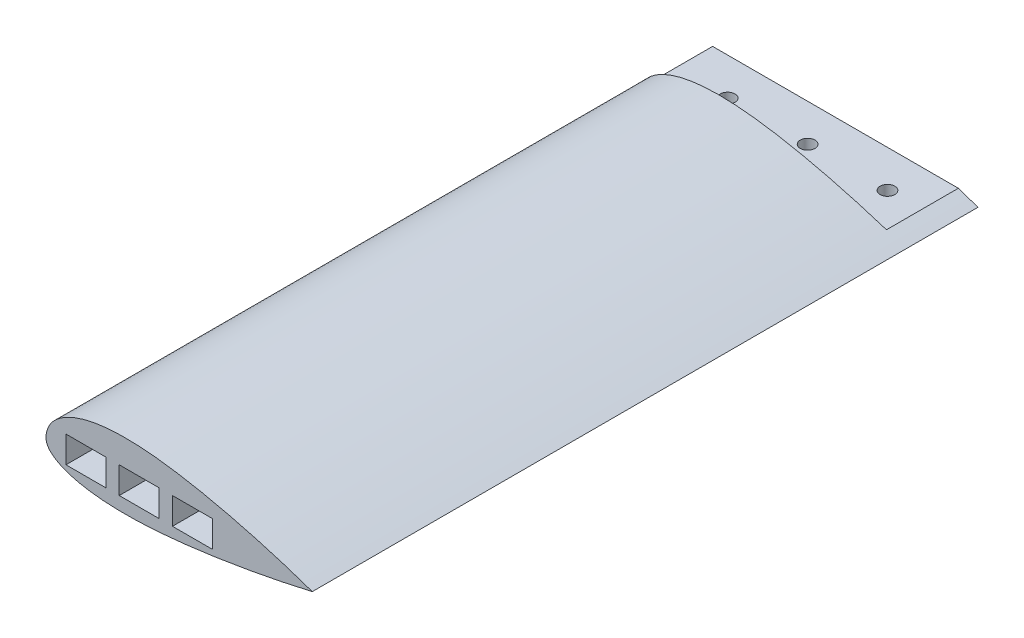
SolidWorks part; units mm, degrees
ref_plane "Front Plane" through (0, 0, 0) normal (0, 0, 1) x (1, 0, 0)
ref_plane "Top Plane" through (0, 0, 0) normal (0, 1, 0) x (1, 0, 0)
ref_plane "Right Plane" through (0, 0, 0) normal (1, 0, 0) x (0, 0, -1)
sketch "Sketch1" plane through (0, 0, 0) normal (0, 0, 1) x (1, 0, 0)
  spline S0 degree 4 poles (0, 0) (0.0009, 0.3297) (0.0295, 0.9275) (0.1439, 1.7967) (0.437, 2.9181) (0.8549, 3.9907) (1.4315, 5.0756) (2.1923, 6.1773) (3.2003, 7.33) (4.4959, 8.5106) (6.154, 9.7149) (8.2741, 10.9292) (10.957, 12.1146) (14.1477, 13.1525) (18.0405, 14.0363) (23.1343, 14.7366) (29.2357, 15.0274) (35.338, 14.8248) (41.1011, 14.3138) (46.841, 13.5968) (51.6037, 12.8505) (56.3456, 11.9834) (61.0671, 11.0139) (64.8328, 10.183) (68.5865, 9.3015) (72.3294, 8.3726) (76.0598, 7.3994) (79.3157, 6.5093) (82.096, 5.721) (84.4127, 5.0444) (86.2537, 4.4957) (88.1107, 3.9294) (89.9289, 3.3646) (91.806, 2.7666) (93.571, 2.1956) (95.5202, 1.5463) (97.1384, 1.0009) (99.1531, 0.3002) (100.3626, -0.127) (101.915, -0.6848) (103.1337, -1.1307) (104.3912, -1.5976) (105.6393, -2.0687) (106.8855, -2.5467) (108.1291, -3.0316) (109.0597, -3.4006) (109.6792, -3.6489) (109.9887, -3.7737) knots 0 0 0 0 0 0.011046 0.020082 0.029326 0.038802 0.04958 0.06121 0.074146 0.090071 0.108265 0.129827 0.155965 0.188307 0.220649 0.263591 0.328276 0.39296 0.425303 0.457645 0.522329 0.554672 0.587014 0.619356 0.651699 0.684041 0.716383 0.748725 0.764896 0.781068 0.797239 0.81341 0.829581 0.845752 0.861923 0.878094 0.894265 0.910437 0.921632 0.932827 0.944023 0.955218 0.966414 0.977609 0.988805 1 1 1 1 1 construction
  spline S1 degree 4 poles (0, 0) (0.0009, 0.3297) (0.0295, 0.9275) (0.1439, 1.7967) (0.437, 2.9181) (0.8549, 3.9907) (1.4315, 5.0756) (2.1923, 6.1773) (3.2003, 7.33) (4.4959, 8.5106) (6.154, 9.7149) (8.2741, 10.9292) (10.957, 12.1146) (14.1477, 13.1525) (18.0405, 14.0363) (23.1343, 14.7366) (29.2357, 15.0274) (35.338, 14.8248) (41.1011, 14.3138) (46.841, 13.5968) (51.6037, 12.8505) (56.3456, 11.9834) (61.0671, 11.0139) (64.8328, 10.183) (68.5865, 9.3015) (72.3294, 8.3726) (76.0598, 7.3994) (79.3157, 6.5093) (82.096, 5.721) (84.4127, 5.0444) (86.2537, 4.4957) (88.1107, 3.9294) (89.9289, 3.3646) (91.806, 2.7666) (93.571, 2.1956) (95.5202, 1.5463) (97.1383, 1.0009) (98.7751, 0.4317) (99.5867, 0.1465) (100.0002, 0) knots 0 0 0 0 0 0.011046 0.020082 0.029326 0.038802 0.04958 0.06121 0.074146 0.090071 0.108265 0.129827 0.155965 0.188307 0.220649 0.263591 0.328276 0.39296 0.425303 0.457645 0.522329 0.554672 0.587014 0.619356 0.651699 0.684041 0.716383 0.748725 0.764896 0.781068 0.797239 0.81341 0.829581 0.845752 0.861923 0.878094 0.894265 0.910434 0.910434 0.910434 0.910434 0.910434
  spline S2 degree 4 poles (0, 0) (0.0003, -0.1693) (0.016, -0.4614) (0.0775, -0.8851) (0.2333, -1.4356) (0.4512, -1.9609) (0.763, -2.5157) (1.1968, -3.1118) (1.8009, -3.7667) (2.6459, -4.4954) (3.845, -5.3152) (5.5202, -6.2106) (7.8905, -7.1807) (10.9471, -8.0963) (15.4296, -9.0396) (21.208, -9.73) (27.9775, -10.0275) (35.6486, -9.8891) (42.3469, -9.4657) (48.0748, -8.9399) (53.7915, -8.3061) (59.4968, -7.5766) (65.1885, -6.7461) (70.8667, -5.8302) (75.5899, -5.0142) (79.3624, -4.3307) (82.6596, -3.7058) (85.4801, -3.1515) (87.5962, -2.7233) (89.0005, -2.4341) (90.1811, -2.1872) (91.104, -1.9926) (92.3051, -1.7354) (93.6554, -1.4439) (95.3898, -1.0596) (97.1027, -0.6748) (99.4365, -0.1347) (101.1191, 0.2637) (103.9947, 0.9599) (105.7889, 1.4169) (107.9207, 1.9617) (109.0082, 2.2534) (109.6995, 2.4359) (109.9984, 2.5166) knots 0 0 0 0 0 0.005887 0.010193 0.014867 0.019889 0.025655 0.032315 0.040498 0.050865 0.064448 0.082823 0.106556 0.139954 0.175459 0.242256 0.309053 0.375849 0.442646 0.476045 0.509443 0.57624 0.643037 0.676435 0.709833 0.743232 0.77663 0.793329 0.810028 0.818378 0.826728 0.835077 0.843427 0.860126 0.876825 0.893524 0.910224 0.932668 0.955112 0.977556 0.988778 1 1 1 1 1 construction
  spline S3 degree 4 poles (0, 0) (0.0003, -0.1693) (0.016, -0.4614) (0.0775, -0.8851) (0.2333, -1.4356) (0.4512, -1.9609) (0.763, -2.5157) (1.1968, -3.1118) (1.8009, -3.7667) (2.6459, -4.4954) (3.845, -5.3152) (5.5202, -6.2106) (7.8905, -7.1807) (10.9471, -8.0963) (15.4296, -9.0396) (21.208, -9.73) (27.9775, -10.0275) (35.6486, -9.8891) (42.3469, -9.4657) (48.0748, -8.9399) (53.7915, -8.3061) (59.4968, -7.5766) (65.1885, -6.7461) (70.8667, -5.8302) (75.5899, -5.0142) (79.3624, -4.3307) (82.6596, -3.7058) (85.4801, -3.1515) (87.5962, -2.7233) (89.0005, -2.4341) (90.1811, -2.1872) (91.104, -1.9926) (92.3051, -1.7354) (93.6554, -1.4439) (95.3898, -1.0596) (97.1027, -0.6748) (98.7145, -0.3018) (99.5756, -0.1002) (100.0002, 0) knots 0 0 0 0 0 0.005887 0.010193 0.014867 0.019889 0.025655 0.032315 0.040498 0.050865 0.064448 0.082823 0.106556 0.139954 0.175459 0.242256 0.309053 0.375849 0.442646 0.476045 0.509443 0.57624 0.643037 0.676435 0.709833 0.743232 0.77663 0.793329 0.810028 0.818378 0.826728 0.835077 0.843427 0.860126 0.876825 0.893524 0.910224 0.910224 0.910224 0.910224 0.910224
sketch "Sketch2" plane through (0, 0, 0) normal (0, 1, 0) x (1, 0, 0)
  line L1 (0, 0) -> (0, -250) construction
  line L2 (0, -250) -> (50, -500) construction
  spline S0 degree 2 poles (0, 0) (0, -250) (50, -500) knots 0 0 0 1 1 1
  dimension "D1" = 250
  dimension "D2" = 250
  dimension "D3" = 50
ref_plane "Plane2" through (0, 0, 500) normal (0, 0, 1) x (1, 0, 0)
sketch "Sketch5" plane through (0, 0, 500) normal (0, 0, 1) x (1, 0, 0)
  spline S0 degree 4 poles (44.9961, 0) (44.997, 0.3297) (45.0257, 0.9275) (45.14, 1.7967) (45.4332, 2.9181) (45.851, 3.9907) (46.4276, 5.0756) (47.1884, 6.1773) (48.1965, 7.33) (49.4921, 8.5106) (51.1502, 9.7149) (53.2702, 10.9292) (55.9531, 12.1146) (59.1438, 13.1525) (63.0366, 14.0363) (68.1305, 14.7366) (74.2318, 15.0274) (80.3341, 14.8248) (86.0972, 14.3138) (91.8371, 13.5968) (96.5999, 12.8505) (101.3417, 11.9834) (106.0633, 11.0139) (109.8289, 10.183) (113.5826, 9.3015) (117.3256, 8.3726) (121.0559, 7.3994) (124.3119, 6.5093) (127.0921, 5.721) (129.4089, 5.0444) (131.2499, 4.4957) (133.1069, 3.9294) (134.9251, 3.3646) (136.8022, 2.7666) (138.5672, 2.1956) (140.5163, 1.5463) (142.1345, 1.0009) (144.1492, 0.3002) (145.3587, -0.127) (146.9111, -0.6848) (148.1299, -1.1307) (149.3874, -1.5976) (150.6354, -2.0687) (151.8817, -2.5467) (153.1253, -3.0316) (154.0559, -3.4006) (154.6753, -3.6489) (154.9848, -3.7737) knots 0 0 0 0 0 0.011046 0.020082 0.029326 0.038802 0.04958 0.06121 0.074146 0.090071 0.108265 0.129827 0.155965 0.188307 0.220649 0.263591 0.328276 0.39296 0.425303 0.457645 0.522329 0.554672 0.587014 0.619356 0.651699 0.684041 0.716383 0.748725 0.764896 0.781068 0.797239 0.81341 0.829581 0.845752 0.861923 0.878094 0.894265 0.910437 0.921632 0.932827 0.944023 0.955218 0.966414 0.977609 0.988805 1 1 1 1 1 construction
  spline S1 degree 4 poles (44.9961, 0) (44.997, 0.3297) (45.0257, 0.9275) (45.14, 1.7967) (45.4332, 2.9181) (45.851, 3.9907) (46.4276, 5.0756) (47.1884, 6.1773) (48.1965, 7.33) (49.4921, 8.5106) (51.1502, 9.7149) (53.2702, 10.9292) (55.9531, 12.1146) (59.1438, 13.1525) (63.0366, 14.0363) (68.1305, 14.7366) (74.2318, 15.0274) (80.3341, 14.8248) (86.0972, 14.3138) (91.8371, 13.5968) (96.5999, 12.8505) (101.3417, 11.9834) (106.0633, 11.0139) (109.8289, 10.183) (113.5826, 9.3015) (117.3256, 8.3726) (121.0559, 7.3994) (124.3119, 6.5093) (127.0921, 5.721) (129.4089, 5.0444) (131.2499, 4.4957) (133.1069, 3.9294) (134.9251, 3.3646) (136.8022, 2.7666) (138.5672, 2.1956) (140.5163, 1.5463) (142.1344, 1.0009) (143.7713, 0.4317) (144.5828, 0.1465) (144.9964, 0) knots 0 0 0 0 0 0.011046 0.020082 0.029326 0.038802 0.04958 0.06121 0.074146 0.090071 0.108265 0.129827 0.155965 0.188307 0.220649 0.263591 0.328276 0.39296 0.425303 0.457645 0.522329 0.554672 0.587014 0.619356 0.651699 0.684041 0.716383 0.748725 0.764896 0.781068 0.797239 0.81341 0.829581 0.845752 0.861923 0.878094 0.894265 0.910434 0.910434 0.910434 0.910434 0.910434 construction
  spline S2 degree 4 poles (44.9961, 0) (44.9964, -0.1693) (45.0121, -0.4614) (45.0736, -0.8851) (45.2294, -1.4356) (45.4474, -1.9609) (45.7592, -2.5157) (46.193, -3.1118) (46.7971, -3.7667) (47.642, -4.4954) (48.8411, -5.3152) (50.5163, -6.2106) (52.8866, -7.1807) (55.9432, -8.0963) (60.4257, -9.0396) (66.2041, -9.73) (72.9737, -10.0275) (80.6447, -9.8891) (87.343, -9.4657) (93.071, -8.9399) (98.7876, -8.3061) (104.493, -7.5766) (110.1846, -6.7461) (115.8628, -5.8302) (120.586, -5.0142) (124.3586, -4.3307) (127.6557, -3.7058) (130.4762, -3.1515) (132.5924, -2.7233) (133.9966, -2.4341) (135.1772, -2.1872) (136.1002, -1.9926) (137.3012, -1.7354) (138.6515, -1.4439) (140.3859, -1.0596) (142.0988, -0.6748) (144.4327, -0.1347) (146.1152, 0.2637) (148.9908, 0.9599) (150.7851, 1.4169) (152.9168, 1.9617) (154.0043, 2.2534) (154.6957, 2.4359) (154.9945, 2.5166) knots 0 0 0 0 0 0.005887 0.010193 0.014867 0.019889 0.025655 0.032315 0.040498 0.050865 0.064448 0.082823 0.106556 0.139954 0.175459 0.242256 0.309053 0.375849 0.442646 0.476045 0.509443 0.57624 0.643037 0.676435 0.709833 0.743232 0.77663 0.793329 0.810028 0.818378 0.826728 0.835077 0.843427 0.860126 0.876825 0.893524 0.910224 0.932668 0.955112 0.977556 0.988778 1 1 1 1 1 construction
  spline S3 degree 4 poles (44.9961, 0) (44.9964, -0.1693) (45.0121, -0.4614) (45.0736, -0.8851) (45.2294, -1.4356) (45.4474, -1.9609) (45.7592, -2.5157) (46.193, -3.1118) (46.7971, -3.7667) (47.642, -4.4954) (48.8411, -5.3152) (50.5163, -6.2106) (52.8866, -7.1807) (55.9432, -8.0963) (60.4257, -9.0396) (66.2041, -9.73) (72.9737, -10.0275) (80.6447, -9.8891) (87.343, -9.4657) (93.071, -8.9399) (98.7876, -8.3061) (104.493, -7.5766) (110.1846, -6.7461) (115.8628, -5.8302) (120.586, -5.0142) (124.3586, -4.3307) (127.6557, -3.7058) (130.4762, -3.1515) (132.5924, -2.7233) (133.9966, -2.4341) (135.1772, -2.1872) (136.1002, -1.9926) (137.3012, -1.7354) (138.6515, -1.4439) (140.3859, -1.0596) (142.0988, -0.6748) (143.7106, -0.3018) (144.5718, -0.1002) (144.9964, 0) knots 0 0 0 0 0 0.005887 0.010193 0.014867 0.019889 0.025655 0.032315 0.040498 0.050865 0.064448 0.082823 0.106556 0.139954 0.175459 0.242256 0.309053 0.375849 0.442646 0.476045 0.509443 0.57624 0.643037 0.676435 0.709833 0.743232 0.77663 0.793329 0.810028 0.818378 0.826728 0.835077 0.843427 0.860126 0.876825 0.893524 0.910224 0.910224 0.910224 0.910224 0.910224 construction
  spline S4 degree 1 poles (50, 0.1659) (125.4884, 0.9751) knots 0 0 1 1 construction
  spline S5 degree 1 poles (50, 0.1659) (125.4884, 0.9751) knots 0 0 1 1 construction
  spline S6 degree 3 poles (50, 0.1659) (50.0179, 0.6032) (50.1757, 1.4567) (50.8242, 2.7316) (51.9666, 4.0552) (54.0561, 5.71) (57.4359, 7.406) (62.0985, 8.7726) (67.0831, 9.581) (73.966, 10.0492) (82.8075, 9.7192) (93.5157, 8.3656) (107.7971, 5.6881) (118.4649, 2.9873) (125.4884, 0.9751) knots 0.003107 0.003107 0.003107 0.003107 0.026472 0.049837 0.073202 0.096568 0.143298 0.190028 0.236758 0.283489 0.376949 0.47041 0.56387 0.750791 0.750791 0.750791 0.750791
  spline S7 degree 3 poles (125.4884, 0.9751) (118.8048, -0.2943) (108.7202, -1.9955) (95.2701, -3.722) (85.1977, -4.6498) (76.8507, -4.9962) (70.2537, -4.8947) (65.3724, -4.5831) (61.4032, -4.0773) (58.338, -3.4825) (56.1227, -2.928) (54.0329, -2.2507) (52.4618, -1.576) (51.3904, -0.9852) (50.7151, -0.5321) (50.3053, -0.1828) (50.0857, 0.053) (50.0309, 0.1225) (50, 0.1659) knots 0.025551 0.025551 0.025551 0.025551 0.205368 0.295277 0.385186 0.475094 0.520049 0.565003 0.609957 0.632435 0.654912 0.677389 0.699866 0.711105 0.722343 0.733582 0.739201 0.74482 0.74482 0.74482 0.74482
  spline S8 degree 1 poles (57.6356, 1.8665) (100.2923, 1.9767) knots 0 0 1 1 construction
  spline S9 degree 1 poles (57.6356, 1.8665) (100.2923, 1.9767) knots 0 0 1 1 construction
  spline S10 degree 3 poles (57.6356, 1.8665) (57.9231, 2.0151) (58.4925, 2.2874) (59.782, 2.82) (61.5543, 3.4029) (63.8869, 3.9672) (67.1912, 4.5347) (71.5938, 4.9175) (77.127, 4.9346) (82.8116, 4.5908) (88.5912, 3.9528) (94.4204, 3.0772) (98.3432, 2.3598) (100.2923, 1.9767) knots 0.118651 0.118651 0.118651 0.118651 0.131754 0.144858 0.171065 0.197272 0.223479 0.275893 0.328307 0.380721 0.433135 0.485549 0.537964 0.537964 0.537964 0.537964
  spline S11 degree 3 poles (100.2923, 1.9767) (98.4159, 1.7345) (94.6502, 1.2813) (87.1702, 0.537) (79.7557, 0.0753) (72.5111, 0.0364) (68.0926, 0.2319) (64.6731, 0.551) (62.1863, 0.8819) (60.2071, 1.2401) (58.6967, 1.5822) (57.9917, 1.7662) (57.6356, 1.8665) knots 0.116889 0.116889 0.116889 0.116889 0.167972 0.219056 0.321223 0.372307 0.42339 0.448932 0.474474 0.500016 0.512787 0.525558 0.525558 0.525558 0.525558
  dimension "D1" = 5
  dimension "D3" = 50
  dimension "D2" = 10
sketch "Sketch6" plane through (0, 0, 0) normal (0, 0, 1) x (1, 0, 0)
  spline S0 degree 4 poles (0, 0) (0.0009, 0.3297) (0.0295, 0.9275) (0.1439, 1.7967) (0.437, 2.9181) (0.8549, 3.9907) (1.4315, 5.0756) (2.1923, 6.1773) (3.2003, 7.33) (4.4959, 8.5106) (6.154, 9.7149) (8.2741, 10.9292) (10.957, 12.1146) (14.1477, 13.1525) (18.0405, 14.0363) (23.1343, 14.7366) (29.2357, 15.0274) (35.338, 14.8248) (41.1011, 14.3138) (46.841, 13.5968) (51.6037, 12.8505) (56.3456, 11.9834) (61.0671, 11.0139) (64.8328, 10.183) (68.5865, 9.3015) (72.3294, 8.3726) (76.0598, 7.3994) (79.3157, 6.5093) (82.096, 5.721) (84.4127, 5.0444) (86.2537, 4.4957) (88.1107, 3.9294) (89.9289, 3.3646) (91.806, 2.7666) (93.571, 2.1956) (95.5202, 1.5463) (97.1384, 1.0009) (99.1531, 0.3002) (100.3626, -0.127) (101.915, -0.6848) (103.1337, -1.1307) (104.3912, -1.5976) (105.6393, -2.0687) (106.8855, -2.5467) (108.1291, -3.0316) (109.0597, -3.4006) (109.6792, -3.6489) (109.9887, -3.7737) knots 0 0 0 0 0 0.011046 0.020082 0.029326 0.038802 0.04958 0.06121 0.074146 0.090071 0.108265 0.129827 0.155965 0.188307 0.220649 0.263591 0.328276 0.39296 0.425303 0.457645 0.522329 0.554672 0.587014 0.619356 0.651699 0.684041 0.716383 0.748725 0.764896 0.781068 0.797239 0.81341 0.829581 0.845752 0.861923 0.878094 0.894265 0.910437 0.921632 0.932827 0.944023 0.955218 0.966414 0.977609 0.988805 1 1 1 1 1 construction
  spline S1 degree 4 poles (0, 0) (0.0009, 0.3297) (0.0295, 0.9275) (0.1439, 1.7967) (0.437, 2.9181) (0.8549, 3.9907) (1.4315, 5.0756) (2.1923, 6.1773) (3.2003, 7.33) (4.4959, 8.5106) (6.154, 9.7149) (8.2741, 10.9292) (10.957, 12.1146) (14.1477, 13.1525) (18.0405, 14.0363) (23.1343, 14.7366) (29.2357, 15.0274) (35.338, 14.8248) (41.1011, 14.3138) (46.841, 13.5968) (51.6037, 12.8505) (56.3456, 11.9834) (61.0671, 11.0139) (64.8328, 10.183) (68.5865, 9.3015) (72.3294, 8.3726) (76.0598, 7.3994) (79.3157, 6.5093) (82.096, 5.721) (84.4127, 5.0444) (86.2537, 4.4957) (88.1107, 3.9294) (89.9289, 3.3646) (91.806, 2.7666) (93.571, 2.1956) (95.5202, 1.5463) (97.1383, 1.0009) (98.7751, 0.4317) (99.5867, 0.1465) (100.0002, 0) knots 0 0 0 0 0 0.011046 0.020082 0.029326 0.038802 0.04958 0.06121 0.074146 0.090071 0.108265 0.129827 0.155965 0.188307 0.220649 0.263591 0.328276 0.39296 0.425303 0.457645 0.522329 0.554672 0.587014 0.619356 0.651699 0.684041 0.716383 0.748725 0.764896 0.781068 0.797239 0.81341 0.829581 0.845752 0.861923 0.878094 0.894265 0.910434 0.910434 0.910434 0.910434 0.910434 construction
  spline S2 degree 4 poles (0, 0) (0.0003, -0.1693) (0.016, -0.4614) (0.0775, -0.8851) (0.2333, -1.4356) (0.4512, -1.9609) (0.763, -2.5157) (1.1968, -3.1118) (1.8009, -3.7667) (2.6459, -4.4954) (3.845, -5.3152) (5.5202, -6.2106) (7.8905, -7.1807) (10.9471, -8.0963) (15.4296, -9.0396) (21.208, -9.73) (27.9775, -10.0275) (35.6486, -9.8891) (42.3469, -9.4657) (48.0748, -8.9399) (53.7915, -8.3061) (59.4968, -7.5766) (65.1885, -6.7461) (70.8667, -5.8302) (75.5899, -5.0142) (79.3624, -4.3307) (82.6596, -3.7058) (85.4801, -3.1515) (87.5962, -2.7233) (89.0005, -2.4341) (90.1811, -2.1872) (91.104, -1.9926) (92.3051, -1.7354) (93.6554, -1.4439) (95.3898, -1.0596) (97.1027, -0.6748) (99.4365, -0.1347) (101.1191, 0.2637) (103.9947, 0.9599) (105.7889, 1.4169) (107.9207, 1.9617) (109.0082, 2.2534) (109.6995, 2.4359) (109.9984, 2.5166) knots 0 0 0 0 0 0.005887 0.010193 0.014867 0.019889 0.025655 0.032315 0.040498 0.050865 0.064448 0.082823 0.106556 0.139954 0.175459 0.242256 0.309053 0.375849 0.442646 0.476045 0.509443 0.57624 0.643037 0.676435 0.709833 0.743232 0.77663 0.793329 0.810028 0.818378 0.826728 0.835077 0.843427 0.860126 0.876825 0.893524 0.910224 0.932668 0.955112 0.977556 0.988778 1 1 1 1 1 construction
  spline S3 degree 4 poles (0, 0) (0.0003, -0.1693) (0.016, -0.4614) (0.0775, -0.8851) (0.2333, -1.4356) (0.4512, -1.9609) (0.763, -2.5157) (1.1968, -3.1118) (1.8009, -3.7667) (2.6459, -4.4954) (3.845, -5.3152) (5.5202, -6.2106) (7.8905, -7.1807) (10.9471, -8.0963) (15.4296, -9.0396) (21.208, -9.73) (27.9775, -10.0275) (35.6486, -9.8891) (42.3469, -9.4657) (48.0748, -8.9399) (53.7915, -8.3061) (59.4968, -7.5766) (65.1885, -6.7461) (70.8667, -5.8302) (75.5899, -5.0142) (79.3624, -4.3307) (82.6596, -3.7058) (85.4801, -3.1515) (87.5962, -2.7233) (89.0005, -2.4341) (90.1811, -2.1872) (91.104, -1.9926) (92.3051, -1.7354) (93.6554, -1.4439) (95.3898, -1.0596) (97.1027, -0.6748) (98.7145, -0.3018) (99.5756, -0.1002) (100.0002, 0) knots 0 0 0 0 0 0.005887 0.010193 0.014867 0.019889 0.025655 0.032315 0.040498 0.050865 0.064448 0.082823 0.106556 0.139954 0.175459 0.242256 0.309053 0.375849 0.442646 0.476045 0.509443 0.57624 0.643037 0.676435 0.709833 0.743232 0.77663 0.793329 0.810028 0.818378 0.826728 0.835077 0.843427 0.860126 0.876825 0.893524 0.910224 0.910224 0.910224 0.910224 0.910224 construction
  spline S4 degree 1 poles (5.0039, 0.1659) (80.4922, 0.9751) knots 0 0 1 1 construction
  spline S5 degree 1 poles (5.0039, 0.1659) (80.4922, 0.9751) knots 0 0 1 1 construction
  spline S6 degree 3 poles (5.0039, 0.1659) (5.0218, 0.6032) (5.1796, 1.4567) (5.8281, 2.7316) (6.9704, 4.0552) (9.0599, 5.71) (12.4398, 7.406) (17.1024, 8.7726) (22.0869, 9.581) (28.9699, 10.0492) (37.8114, 9.7192) (48.5196, 8.3656) (62.801, 5.6881) (73.4687, 2.9873) (80.4922, 0.9751) knots 0.003107 0.003107 0.003107 0.003107 0.026472 0.049837 0.073202 0.096568 0.143298 0.190028 0.236758 0.283489 0.376949 0.47041 0.56387 0.750791 0.750791 0.750791 0.750791
  spline S7 degree 3 poles (80.4922, 0.9751) (73.8087, -0.2943) (63.7241, -1.9955) (50.274, -3.722) (40.2016, -4.6498) (31.8546, -4.9962) (25.2576, -4.8947) (20.3763, -4.5831) (16.407, -4.0773) (13.3418, -3.4825) (11.1266, -2.928) (9.0368, -2.2507) (7.4657, -1.576) (6.3942, -0.9852) (5.719, -0.5321) (5.3091, -0.1828) (5.0896, 0.053) (5.0347, 0.1225) (5.0039, 0.1659) knots 0.025551 0.025551 0.025551 0.025551 0.205368 0.295277 0.385186 0.475094 0.520049 0.565003 0.609957 0.632435 0.654912 0.677389 0.699866 0.711105 0.722343 0.733582 0.739201 0.74482 0.74482 0.74482 0.74482
  dimension "D1" = 5
extrude "Boss-Extrude1" add sketch "Sketch1" along normal mid plane 250
extrude "Cut-Extrude1" cut sketch "Sketch6" against normal blind 90 and the other way blind 110
sketch "Sketch9" plane through (0, 0, -125) normal (0, 0, 1) x (1, 0, 0)
  line L1 (0, 2.5) -> (100, 2.5)
  line L2 (0, 2.5) -> (0, -2.5)
  line L3 (0, -2.5) -> (100, -2.5)
  line L4 (100, 2.5) -> (100, -2.5)
  point P4 (0, 0)
  dimension "D1" = 100
  dimension "D2" = 5
extrude "Cut-Extrude2" cut sketch "Sketch9" along normal blind 27 flip side to cut contours L1 L4 L3 L2
hole_wizard "M5 Clearance Hole1" positions "Sketch13" profile "Sketch14" hole size "M5" standard "ISO" end condition through all
sketch "Sketch13" plane through (0, 2.5, 0) normal (0, 1, 0) x (1, 0, 0)
  line L7 (0.3394, 98) -> (92.6266, 98) construction
  line L8 (92.6266, 98) -> (0.3394, 98) construction
  line L10 (100.0002, -125) -> (100.0002, 98) construction
  point P0 (20.0002, 111)
  point P4 (80.0002, 111)
  point P6 (80.0002, 111)
  point P30 (50.0002, 111)
  dimension "D1" = 30
  dimension "D2" = 50
  dimension "D3" = 13
  dimension "D4" = 13
  dimension "D5" = 30
sketch "Sketch14" plane through (20.0002, 2.5, -111) normal (1, 0, 0) x (0, 0, 1)
  line L0 (0, 0) -> (0, 12.5275)
  line L1 (0, 12.5275) -> (2.75, 12.5275)
  line L2 (2.75, 12.5275) -> (2.75, 0)
  line L5 (2.75, 0) -> (0, 0)
  line L11 (0, -6.35) -> (0, 107.95) construction
  dimension "Thru Hole Dia." = 5.5
  dimension "Thru Hole Depth" = 12.5275
sketch "Sketch15" plane through (0, 0, 125) normal (0, 0, 1) x (1, 0, 0)
  line L1 (27.5, -5) -> (42.5, -5)
  line L2 (27.5, -5) -> (27.5, 5)
  line L3 (27.5, 5) -> (42.5, 5)
  line L4 (42.5, -5) -> (42.5, 5)
  line L5 (22.5, 5) -> (7.5, 5)
  line L6 (22.5, 5) -> (22.5, -5)
  line L7 (22.5, -5) -> (7.5, -5)
  line L8 (7.5, 5) -> (7.5, -5)
  line L9 (47.5, 5) -> (62.5, 5)
  line L10 (47.5, 5) -> (47.5, -5)
  line L11 (47.5, -5) -> (62.5, -5)
  line L12 (62.5, 5) -> (62.5, -5)
  point P4 (35, 5)
  point P5 (42.5, 0)
  point P12 (22.5, 0)
  point P17 (62.5, 0)
  dimension "D1" = 35
  dimension "D2" = 15
  dimension "D3" = 10
  dimension "D4" = 15
  dimension "D5" = 10
  dimension "D6" = 5
  dimension "D7" = 15
  dimension "D8" = 10
  dimension "D9" = 5
extrude "Cut-Extrude3" cut sketch "Sketch15" against normal blind 10
